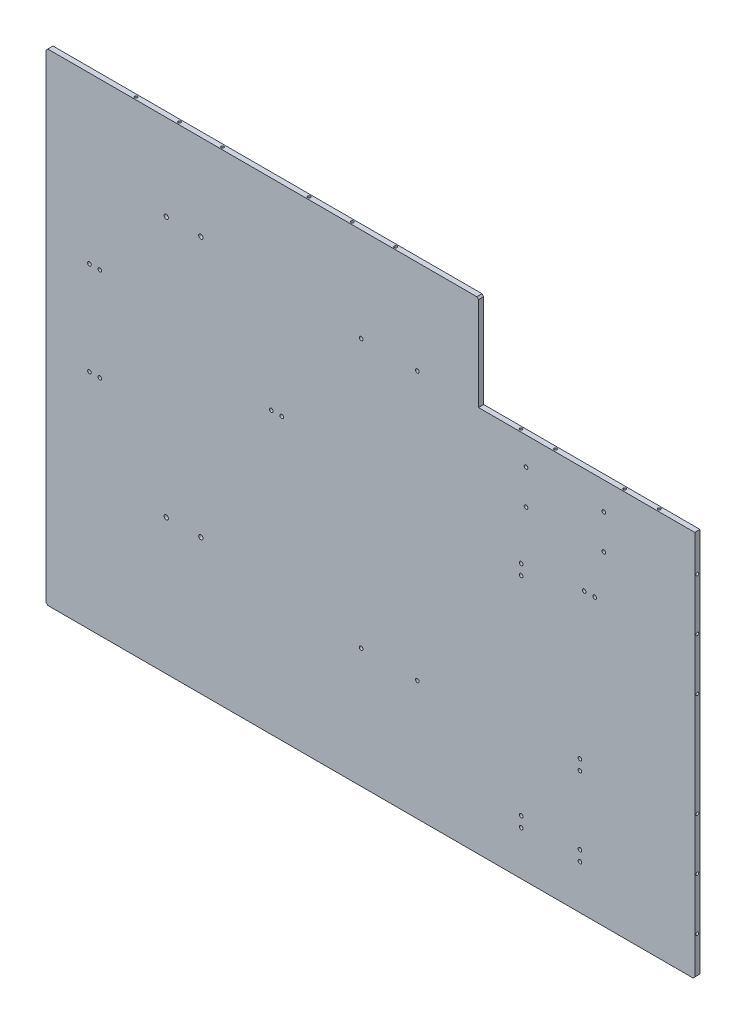
SolidWorks part; units mm, degrees
ref_plane "前视基准面" through (0, 0, 0) normal (0, 0, 1) x (1, 0, 0)
ref_plane "上视基准面" through (0, 0, 0) normal (0, 1, 0) x (1, 0, 0)
ref_plane "右视基准面" through (0, 0, 0) normal (1, 0, 0) x (0, 0, -1)
sketch "草图1" plane through (0, 0, 0) normal (0, 0, 1) x (1, 0, 0)
  line L1 (0, 0) -> (610, 0)
  line L2 (0, 0) -> (0, 420)
  line L3 (0, 420) -> (610, 420)
  line L4 (610, 0) -> (610, 420)
  dimension "D1" = 610
  dimension "D2" = 420
extrude "凸台-拉伸1" add sketch "草图1" along normal blind 6
hole_wizard "M6 螺纹孔1" positions "草图2" profile "草图3" tap size "M6" standard "ISO"
sketch "草图2" plane through (0, 0, 6) normal (0, 0, 1) x (1, 0, 0)
  point P0 (99, 410.6)
  point P3 (139, 410.6)
sketch "草图3" plane through (99, 410.6, 6) normal (1, 0, 0) x (0, -1, 0)
  line L0 (0, 0) -> (0, 16.5022)
  line L1 (0, 16.5022) -> (2.5, 15)
  line L2 (2.5, 15) -> (2.5, 0)
  line L5 (2.5, 0) -> (0, 0)
  line L10 (0, 16.5022) -> (-2.5, 15) construction
  line L11 (0, -6.35) -> (0, 107.95) construction
  dimension "螺纹孔钻头直径" = 5
  dimension "螺纹孔钻头深度" = 15
  dimension "导头角度" = 118
cosmetic thread "孔螺蚊线1" parameters "D1"=6, "D2"=6
cosmetic thread "孔螺蚊线2" parameters "D1"=6, "D2"=6
hole_wizard "M5 螺纹孔1" positions "草图4" profile "草图5" tap size "M5" standard "ISO"
sketch "草图4" plane through (0, 0, 6) normal (0, 0, 1) x (1, 0, 0)
  point P0 (10.2316, 318.9)
  point P3 (22.2316, 318.9)
sketch "草图5" plane through (10.2316, 318.9, 6) normal (1, 0, 0) x (0, -1, 0)
  line L0 (0, 0) -> (0, 13.6618)
  line L1 (0, 13.6618) -> (2.1, 12.4)
  line L2 (2.1, 12.4) -> (2.1, 0)
  line L5 (2.1, 0) -> (0, 0)
  line L10 (0, 13.6618) -> (-2.1, 12.4) construction
  line L11 (0, -6.35) -> (0, 107.95) construction
  dimension "螺纹孔钻头直径" = 4.2
  dimension "螺纹孔钻头深度" = 12.4
  dimension "导头角度" = 118
cosmetic thread "孔螺蚊线3" parameters "D1"=6, "D2"=5
cosmetic thread "孔螺蚊线4" parameters "D1"=6, "D2"=5
hole_wizard "M5 螺纹孔2" positions "草图6" profile "草图7" tap size "M5" standard "ISO"
sketch "草图6" plane through (0, 0, 6) normal (0, 0, 1) x (1, 0, 0)
  point P0 (10.2316, 210.9)
  point P3 (22.2316, 210.9)
sketch "草图7" plane through (10.2316, 210.9, 6) normal (1, 0, 0) x (0, -1, 0)
  line L0 (0, 0) -> (0, 13.6618)
  line L1 (0, 13.6618) -> (2.1, 12.4)
  line L2 (2.1, 12.4) -> (2.1, 0)
  line L5 (2.1, 0) -> (0, 0)
  line L10 (0, 13.6618) -> (-2.1, 12.4) construction
  line L11 (0, -6.35) -> (0, 107.95) construction
  dimension "螺纹孔钻头直径" = 4.2
  dimension "螺纹孔钻头深度" = 12.4
  dimension "导头角度" = 118
cosmetic thread "孔螺蚊线5" parameters "D1"=6, "D2"=5
cosmetic thread "孔螺蚊线6" parameters "D1"=6, "D2"=5
hole_wizard "M6 螺纹孔2" positions "草图8" profile "草图9" tap size "M6" standard "ISO"
sketch "草图8" plane through (0, 0, 6) normal (0, 0, 1) x (1, 0, 0)
  point P0 (99, 109.6)
  point P3 (139, 109.6)
sketch "草图9" plane through (99, 109.6, 6) normal (1, 0, 0) x (0, -1, 0)
  line L0 (0, 0) -> (0, 16.5022)
  line L1 (0, 16.5022) -> (2.5, 15)
  line L2 (2.5, 15) -> (2.5, 0)
  line L5 (2.5, 0) -> (0, 0)
  line L10 (0, 16.5022) -> (-2.5, 15) construction
  line L11 (0, -6.35) -> (0, 107.95) construction
  dimension "螺纹孔钻头直径" = 5
  dimension "螺纹孔钻头深度" = 15
  dimension "导头角度" = 118
cosmetic thread "孔螺蚊线7" parameters "D1"=6, "D2"=6
cosmetic thread "孔螺蚊线8" parameters "D1"=6, "D2"=6
hole_wizard "M5 螺纹孔3" positions "草图12" profile "草图13" tap size "M5" standard "ISO"
sketch "草图12" plane through (0, 0, 6) normal (0, 0, 1) x (1, 0, 0)
  point P0 (515, 367.9)
  point P3 (515, 327.9)
  point P6 (605, 327.9)
  point P9 (605, 367.9)
sketch "草图13" plane through (515, 367.9, 6) normal (1, 0, 0) x (0, -1, 0)
  line L0 (0, 0) -> (0, 13.6618)
  line L1 (0, 13.6618) -> (2.1, 12.4)
  line L2 (2.1, 12.4) -> (2.1, 0)
  line L5 (2.1, 0) -> (0, 0)
  line L10 (0, 13.6618) -> (-2.1, 12.4) construction
  line L11 (0, -6.35) -> (0, 107.95) construction
  dimension "螺纹孔钻头直径" = 4.2
  dimension "螺纹孔钻头深度" = 12.4
  dimension "导头角度" = 118
cosmetic thread "孔螺蚊线29" parameters "D1"=6, "D2"=5
cosmetic thread "孔螺蚊线30" parameters "D1"=6, "D2"=5
cosmetic thread "孔螺蚊线31" parameters "D1"=6, "D2"=5
cosmetic thread "孔螺蚊线32" parameters "D1"=6, "D2"=5
hole_wizard "M5 螺纹孔4" positions "草图14" profile "草图15" tap size "M5" standard "ISO"
sketch "草图14" plane through (0, 0, 6) normal (0, 0, 1) x (1, 0, 0)
  point P0 (582.2316, 277.4)
  point P3 (594.2316, 277.4)
  point P6 (509.3, 268.5)
  point P9 (509.3, 256.5)
  point P12 (509.3, 16)
  point P15 (509.3, 4)
  point P18 (577.3, 16)
  point P21 (577.3, 4)
  point P24 (577.3, 95)
  point P27 (577.3, 107)
sketch "草图15" plane through (582.2316, 277.4, 6) normal (1, 0, 0) x (0, -1, 0)
  line L0 (0, 0) -> (0, 13.6618)
  line L1 (0, 13.6618) -> (2.1, 12.4)
  line L2 (2.1, 12.4) -> (2.1, 0)
  line L5 (2.1, 0) -> (0, 0)
  line L10 (0, 13.6618) -> (-2.1, 12.4) construction
  line L11 (0, -6.35) -> (0, 107.95) construction
  dimension "螺纹孔钻头直径" = 4.2
  dimension "螺纹孔钻头深度" = 12.4
  dimension "导头角度" = 118
cosmetic thread "孔螺蚊线13" parameters "D1"=6, "D2"=5
cosmetic thread "孔螺蚊线14" parameters "D1"=6, "D2"=5
cosmetic thread "孔螺蚊线15" parameters "D1"=6, "D2"=5
cosmetic thread "孔螺蚊线16" parameters "D1"=6, "D2"=5
cosmetic thread "孔螺蚊线17" parameters "D1"=6, "D2"=5
cosmetic thread "孔螺蚊线18" parameters "D1"=6, "D2"=5
cosmetic thread "孔螺蚊线19" parameters "D1"=6, "D2"=5
cosmetic thread "孔螺蚊线20" parameters "D1"=6, "D2"=5
cosmetic thread "孔螺蚊线21" parameters "D1"=6, "D2"=5
cosmetic thread "孔螺蚊线22" parameters "D1"=6, "D2"=5
hole_wizard "M5 螺纹孔5" positions "草图16" profile "草图17" tap size "M5" standard "ISO"
sketch "草图16" plane through (0, 0, 6) normal (0, 0, 1) x (1, 0, 0)
  point P0 (220.5202, 277.4)
  point P3 (232.5202, 277.4)
sketch "草图17" plane through (220.5202, 277.4, 6) normal (1, 0, 0) x (0, -1, 0)
  line L0 (0, 0) -> (0, 13.6618)
  line L1 (0, 13.6618) -> (2.1, 12.4)
  line L2 (2.1, 12.4) -> (2.1, 0)
  line L5 (2.1, 0) -> (0, 0)
  line L10 (0, 13.6618) -> (-2.1, 12.4) construction
  line L11 (0, -6.35) -> (0, 107.95) construction
  dimension "螺纹孔钻头直径" = 4.2
  dimension "螺纹孔钻头深度" = 12.4
  dimension "导头角度" = 118
cosmetic thread "孔螺蚊线23" parameters "D1"=6, "D2"=5
cosmetic thread "孔螺蚊线24" parameters "D1"=6, "D2"=5
hole_wizard "M5 螺纹孔6" positions "草图18" profile "草图19" tap size "M5" standard "ISO"
sketch "草图18" plane through (0, 0, 6) normal (0, 0, 1) x (1, 0, 0)
  point P0 (324.3073, 91.2147)
  point P3 (389.3073, 91.2147)
sketch "草图19" plane through (324.3073, 91.2147, 6) normal (1, 0, 0) x (0, -1, 0)
  line L0 (0, 0) -> (0, 13.6618)
  line L1 (0, 13.6618) -> (2.1, 12.4)
  line L2 (2.1, 12.4) -> (2.1, 0)
  line L5 (2.1, 0) -> (0, 0)
  line L10 (0, 13.6618) -> (-2.1, 12.4) construction
  line L11 (0, -6.35) -> (0, 107.95) construction
  dimension "螺纹孔钻头直径" = 4.2
  dimension "螺纹孔钻头深度" = 12.4
  dimension "导头角度" = 118
cosmetic thread "孔螺蚊线25" parameters "D1"=6, "D2"=5
cosmetic thread "孔螺蚊线26" parameters "D1"=6, "D2"=5
hole_wizard "M5 螺纹孔7" positions "草图20" profile "草图21" tap size "M5" standard "ISO"
sketch "草图20" plane through (0, 0, 6) normal (0, 0, 1) x (1, 0, 0)
  point P0 (324.3073, 401.2147)
  point P3 (389.3073, 401.2147)
sketch "草图21" plane through (324.3073, 401.2147, 6) normal (1, 0, 0) x (0, -1, 0)
  line L0 (0, 0) -> (0, 13.6618)
  line L1 (0, 13.6618) -> (2.1, 12.4)
  line L2 (2.1, 12.4) -> (2.1, 0)
  line L5 (2.1, 0) -> (0, 0)
  line L10 (0, 13.6618) -> (-2.1, 12.4) construction
  line L11 (0, -6.35) -> (0, 107.95) construction
  dimension "螺纹孔钻头直径" = 4.2
  dimension "螺纹孔钻头深度" = 12.4
  dimension "导头角度" = 118
cosmetic thread "孔螺蚊线27" parameters "D1"=6, "D2"=5
cosmetic thread "孔螺蚊线28" parameters "D1"=6, "D2"=5
sketch "草图22" plane through (0, 0, 0) normal (0, -1, 0) x (1, 0, 0)
  line L1 (0, 0) -> (610, 0)
  line L2 (0, 0) -> (0, 6)
  line L3 (0, 6) -> (610, 6)
  line L4 (610, 0) -> (610, 6)
extrude "凸台-拉伸2" add sketch "草图22" along normal blind 47.17
sketch "草图23" plane through (0, 420, 0) normal (0, 1, 0) x (1, 0, 0)
  line L1 (610, -6) -> (0, -6)
  line L2 (610, -6) -> (610, 0)
  line L3 (610, 0) -> (0, 0)
  line L4 (0, -6) -> (0, 0)
extrude "凸台-拉伸3" add sketch "草图23" along normal blind 90
sketch "草图24" plane through (0, 0, 0) normal (-1, 0, 0) x (0, 0, 1)
  line L1 (6, 510) -> (0, 510)
  line L2 (6, 510) -> (6, -47.17)
  line L3 (6, -47.17) -> (0, -47.17)
  line L4 (0, 510) -> (0, -47.17)
extrude "凸台-拉伸4" add sketch "草图24" along normal blind 39.94
sketch "草图25" plane through (610, 0, 0) normal (1, 0, 0) x (0, 0, -1)
  line L1 (-6, -47.17) -> (0, -47.17)
  line L2 (-6, -47.17) -> (-6, 510)
  line L3 (-6, 510) -> (0, 510)
  line L4 (0, -47.17) -> (0, 510)
extrude "凸台-拉伸5" add sketch "草图25" along normal blind 100.06
sketch "草图26" plane through (0, 0, 6) normal (0, 0, 1) x (1, 0, 0)
  line L1 (710.06, 510) -> (460.06, 510)
  line L2 (710.06, 510) -> (710.06, 400)
  line L3 (710.06, 400) -> (460.06, 400)
  line L4 (460.06, 510) -> (460.06, 400)
  dimension "D1" = 250
  dimension "D2" = 110
extrude "切除-拉伸1" cut sketch "草图26" against normal blind 100.06
chamfer "倒角2" distance 2 angle 45 1 edges at (710.06, -47.17, 3)
chamfer "倒角3" distance 2 angle 45 1 edges at (-39.94, -47.17, 3)
chamfer "倒角4" distance 2 angle 45 1 edges at (-39.94, 510, 3)
chamfer "倒角5" distance 2 angle 45 1 edges at (460.06, 510, 3)
hole_wizard "M4 螺纹孔1" positions "草图27" profile "草图28" tap size "M4" standard "ISO"
sketch "草图27" plane through (0, -47.17, 0) normal (0, -1, 0) x (-1, 0, 0)
  point P0 (-35.0616, -3)
  point P3 (-135.0616, -3)
  point P6 (-235.0616, -3)
  point P9 (-435.0616, -3)
  point P12 (-535.0616, -3)
  point P15 (-635.0616, -3)
sketch "草图28" plane through (35.0616, -47.17, 3) normal (1, 0, 0) x (0, 0, -1)
  line L0 (0, 0) -> (0, 11.0914)
  line L1 (0, 11.0914) -> (1.65, 10.1)
  line L2 (1.65, 10.1) -> (1.65, 0)
  line L5 (1.65, 0) -> (0, 0)
  line L10 (0, 11.0914) -> (-1.65, 10.1) construction
  line L11 (0, -6.35) -> (0, 107.95) construction
  dimension "螺纹孔钻头直径" = 3.3
  dimension "螺纹孔钻头深度" = 10.1
  dimension "导头角度" = 118
cosmetic thread "孔螺蚊线33"
cosmetic thread "孔螺蚊线34"
cosmetic thread "孔螺蚊线35"
cosmetic thread "孔螺蚊线36"
cosmetic thread "孔螺蚊线37"
cosmetic thread "孔螺蚊线38"
hole_wizard "M4 螺纹孔2" positions "草图29" profile "草图30" tap size "M4" standard "ISO"
sketch "草图29" plane through (-39.94, 0, 0) normal (-1, 0, 0) x (0, 0, 1)
  point P0 (3, 471.4166)
  point P3 (3, 391.4166)
  point P6 (3, 311.4166)
  point P9 (3, 151.4166)
  point P12 (3, 71.4166)
  point P15 (3, -8.5834)
sketch "草图30" plane through (-39.94, 471.4166, 3) normal (0, 1, 0) x (0, 0, 1)
  line L0 (0, 0) -> (0, 11.0914)
  line L1 (0, 11.0914) -> (1.65, 10.1)
  line L2 (1.65, 10.1) -> (1.65, 0)
  line L5 (1.65, 0) -> (0, 0)
  line L10 (0, 11.0914) -> (-1.65, 10.1) construction
  line L11 (0, -6.35) -> (0, 107.95) construction
  dimension "螺纹孔钻头直径" = 3.3
  dimension "螺纹孔钻头深度" = 10.1
  dimension "导头角度" = 118
cosmetic thread "孔螺蚊线39"
cosmetic thread "孔螺蚊线40"
cosmetic thread "孔螺蚊线41"
cosmetic thread "孔螺蚊线42"
cosmetic thread "孔螺蚊线43"
cosmetic thread "孔螺蚊线44"
hole_wizard "M4 螺纹孔3" positions "草图31" profile "草图32" tap size "M4" standard "ISO"
sketch "草图31" plane through (0, 510, 0) normal (0, 1, 0) x (1, 0, 0)
  point P0 (361.1799, -3)
  point P3 (311.1799, -3)
  point P6 (261.1799, -3)
  point P9 (161.1799, -3)
  point P12 (111.1799, -3)
  point P15 (61.1799, -3)
sketch "草图32" plane through (361.1799, 510, 3) normal (1, 0, 0) x (0, 0, 1)
  line L0 (0, 0) -> (0, 11.0914)
  line L1 (0, 11.0914) -> (1.65, 10.1)
  line L2 (1.65, 10.1) -> (1.65, 0)
  line L5 (1.65, 0) -> (0, 0)
  line L10 (0, 11.0914) -> (-1.65, 10.1) construction
  line L11 (0, -6.35) -> (0, 107.95) construction
  dimension "螺纹孔钻头直径" = 3.3
  dimension "螺纹孔钻头深度" = 10.1
  dimension "导头角度" = 118
cosmetic thread "孔螺蚊线45"
cosmetic thread "孔螺蚊线46"
cosmetic thread "孔螺蚊线47"
cosmetic thread "孔螺蚊线48"
cosmetic thread "孔螺蚊线49"
cosmetic thread "孔螺蚊线50"
hole_wizard "M4 螺纹孔4" positions "草图33" profile "草图34" tap size "M4" standard "ISO"
sketch "草图33" plane through (710.06, 0, 0) normal (1, 0, 0) x (0, 0, -1)
  point P0 (-3, -3.2184)
  point P3 (-3, 56.7816)
  point P6 (-3, 116.7816)
  point P9 (-3, 236.7816)
  point P12 (-3, 296.7816)
  point P15 (-3, 356.7816)
sketch "草图34" plane through (710.06, -3.2184, 3) normal (0, 1, 0) x (0, 0, -1)
  line L0 (0, 0) -> (0, 11.0914)
  line L1 (0, 11.0914) -> (1.65, 10.1)
  line L2 (1.65, 10.1) -> (1.65, 0)
  line L5 (1.65, 0) -> (0, 0)
  line L10 (0, 11.0914) -> (-1.65, 10.1) construction
  line L11 (0, -6.35) -> (0, 107.95) construction
  dimension "螺纹孔钻头直径" = 3.3
  dimension "螺纹孔钻头深度" = 10.1
  dimension "导头角度" = 118
cosmetic thread "孔螺蚊线51"
cosmetic thread "孔螺蚊线52"
cosmetic thread "孔螺蚊线53"
cosmetic thread "孔螺蚊线54"
cosmetic thread "孔螺蚊线55"
cosmetic thread "孔螺蚊线56"
hole_wizard "M4 螺纹孔5" positions "草图35" profile "草图36" tap size "M4" standard "ISO"
sketch "草图35" plane through (0, 400, 0) normal (0, 1, 0) x (1, 0, 0)
  point P0 (666.0616, -3)
  point P3 (626.0616, -3)
  point P6 (546.0616, -3)
  point P9 (506.0616, -3)
sketch "草图36" plane through (666.0616, 400, 3) normal (1, 0, 0) x (0, 0, 1)
  line L0 (0, 0) -> (0, 11.0914)
  line L1 (0, 11.0914) -> (1.65, 10.1)
  line L2 (1.65, 10.1) -> (1.65, 0)
  line L5 (1.65, 0) -> (0, 0)
  line L10 (0, 11.0914) -> (-1.65, 10.1) construction
  line L11 (0, -6.35) -> (0, 107.95) construction
  dimension "螺纹孔钻头直径" = 3.3
  dimension "螺纹孔钻头深度" = 10.1
  dimension "导头角度" = 118
cosmetic thread "孔螺蚊线57"
cosmetic thread "孔螺蚊线58"
cosmetic thread "孔螺蚊线59"
cosmetic thread "孔螺蚊线60"
